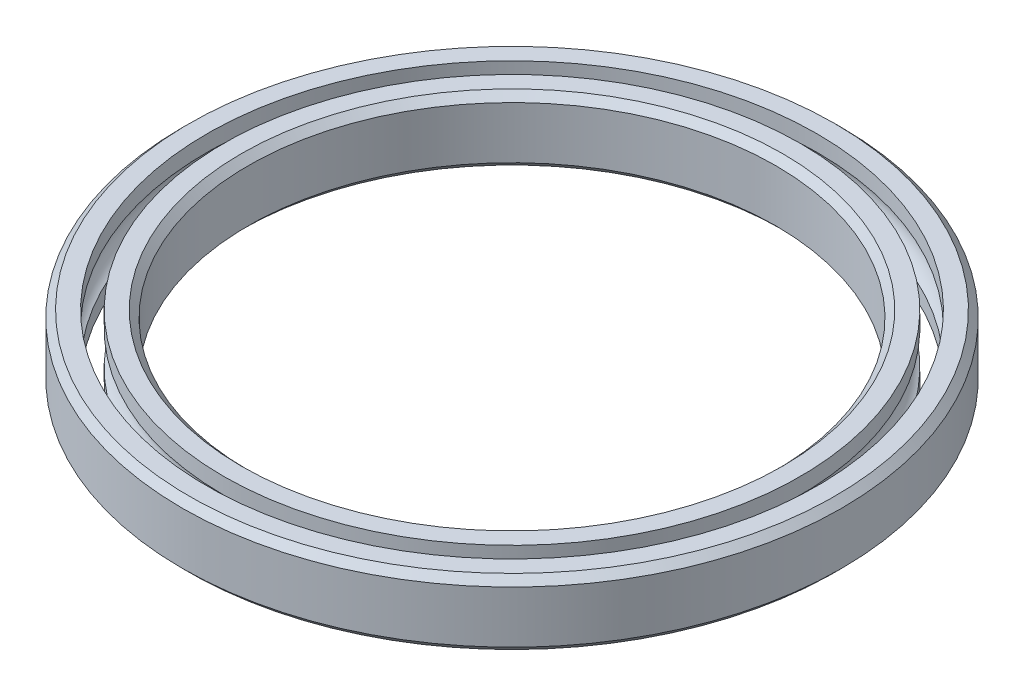
SolidWorks part; units mm, degrees
ref_plane "Front Plane" through (0, 0, 0) normal (0, 0, 1) x (1, 0, 0)
ref_plane "Top Plane" through (0, 0, 0) normal (0, 1, 0) x (1, 0, 0)
ref_plane "Right Plane" through (0, 0, 0) normal (1, 0, 0) x (0, 0, -1)
sketch "Sketch1" plane through (0, 0, 0) normal (0, 0, 1) x (1, 0, 0)
  line L0 (0, 0) -> (0, 30.3339) construction
  line L1 (-23.8125, -1.8812) -> (-23.8125, 1.8812)
  line L2 (-23.8125, 1.8812) -> (-23.3125, 2.3813)
  line L3 (-23.8125, -1.8812) -> (-23.3125, -2.3813)
  line L4 (-23.3125, -2.3813) -> (-22.0345, -2.3813)
  line L5 (-22.0345, -2.3813) -> (-22.0345, -1.218)
  line L6 (-23.3125, 2.3813) -> (-22.0345, 2.3813)
  line L7 (-23.8125, 0) -> (0, 0) construction
  line L8 (-22.0345, 2.3813) -> (-22.0345, 1.218)
  line L9 (-21.4312, 2.3813) -> (-21.4312, 0) construction
  line L10 (-19.05, -1.8812) -> (-19.55, -2.3812)
  line L11 (-19.55, -2.3812) -> (-20.828, -2.3813)
  line L12 (-20.828, -2.3813) -> (-20.828, -1.218)
  line L13 (-19.05, -1.8812) -> (-19.05, 1.8812)
  line L14 (-19.05, 1.8812) -> (-19.55, 2.3812)
  line L15 (-20.828, 2.3813) -> (-20.828, 1.218)
  line L16 (-19.55, 2.3812) -> (-20.828, 2.3813)
  arc A0 (-22.0345, -1.218) -> (-22.0345, 1.218) centre (-21.4312, 0) cw
  arc A1 (-20.828, -1.218) -> (-20.828, 1.218) centre (-21.4312, 0) ccw
  dimension "D1" = 135
  dimension "D2" = 4.7625
  dimension "D3" = 22.0345
  dimension "D4" = 23.8125
  dimension "D5" = 0.5
  dimension "D6" = 19.05
revolve "Revolve1" add sketch "Sketch1" angle 360 about L0
